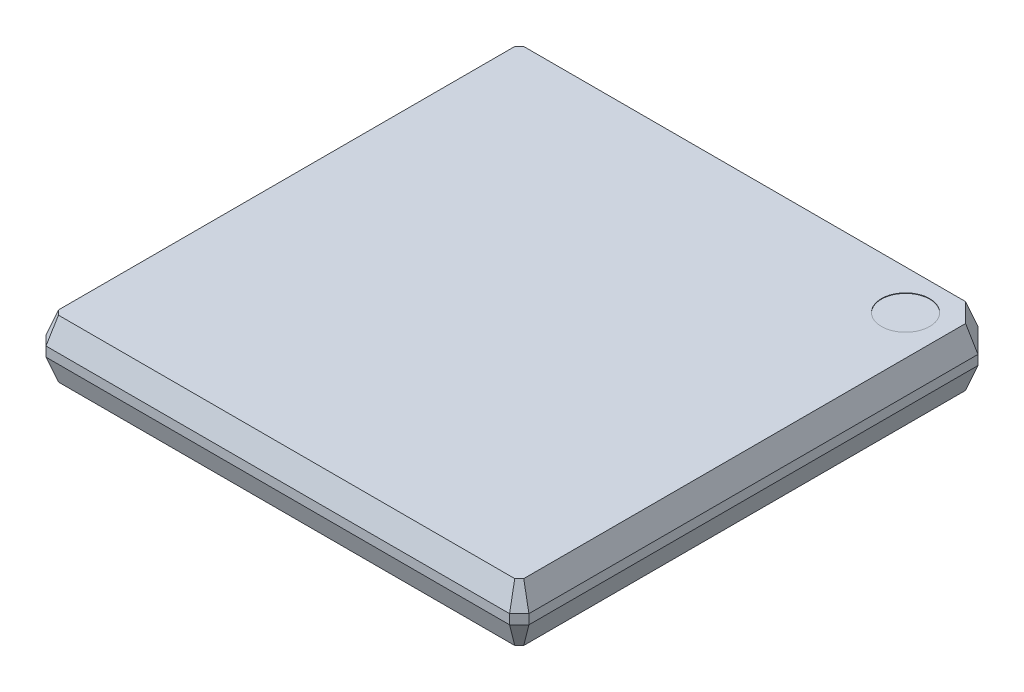
SolidWorks part; units mm, degrees
ref_plane "Front Plane" through (0, 0, 0) normal (0, 0, 1) x (1, 0, 0)
ref_plane "Top Plane" through (0, 0, 0) normal (0, 1, 0) x (1, 0, 0)
ref_plane "Right Plane" through (0, 0, 0) normal (1, 0, 0) x (0, 0, -1)
sketch "Sketch1" plane through (0, 0, 0) normal (0, 1, 0) x (1, 0, 0)
  line L1 (-5, -5) -> (5, -5)
  line L2 (-5, -5) -> (-5, 5)
  line L3 (-5, 5) -> (5, 5)
  line L4 (5, -5) -> (5, 5)
  line L5 (-5, -5) -> (5, 5) construction
  line L6 (-5, 5) -> (5, -5) construction
  point P0 (0, 0)
  dimension "D1" = 10
extrude "Boss-Extrude1" add sketch "Sketch1" along normal mid plane 0.2
chamfer "Chamfer1" distance 0.2 angle 45 3 edges at (5, 0, 5) (-5, 0, 5) (-5, 0, -5)
chamfer "Chamfer2" distance 0.5 angle 45 1 edges at (5, 0, -5)
sketch "Sketch2" plane through (0, 0.1, 0) normal (0, 1, 0) x (1, 0, 0)
  line L0 (-4.8, 5) -> (-5, 4.8)
  line L1 (-5, 4.8) -> (-5, -4.8)
  line L2 (-5, -4.8) -> (-4.8, -5)
  line L3 (-4.8, -5) -> (4.8, -5)
  line L4 (4.8, -5) -> (5, -4.8)
  line L5 (5, -4.8) -> (5, 4.5)
  line L6 (5, 4.5) -> (4.5, 5)
  line L7 (4.5, 5) -> (-4.8, 5)
extrude "Boss-Extrude2" add sketch "Sketch2" along normal blind 0.5 draft 20
mirror "Mirror1" about plane through (0, 0, 0) normal (0, 1, 0) of "Boss-Extrude2"
sketch "Sketch3" plane through (0, 0.6, 0) normal (0, 1, 0) x (1, 0, 0)
  line L0 (0, -0.66) -> (0, 0.66) construction
  line L1 (-0.66, 0) -> (0.66, 0) construction
  circle A0 centre (4, 4) radius 0.5
  dimension "D1" = 1
  dimension "D2" = 4
  dimension "D3" = 4
extrude "Cut-Extrude1" cut sketch "Sketch3" against normal blind 0.01
